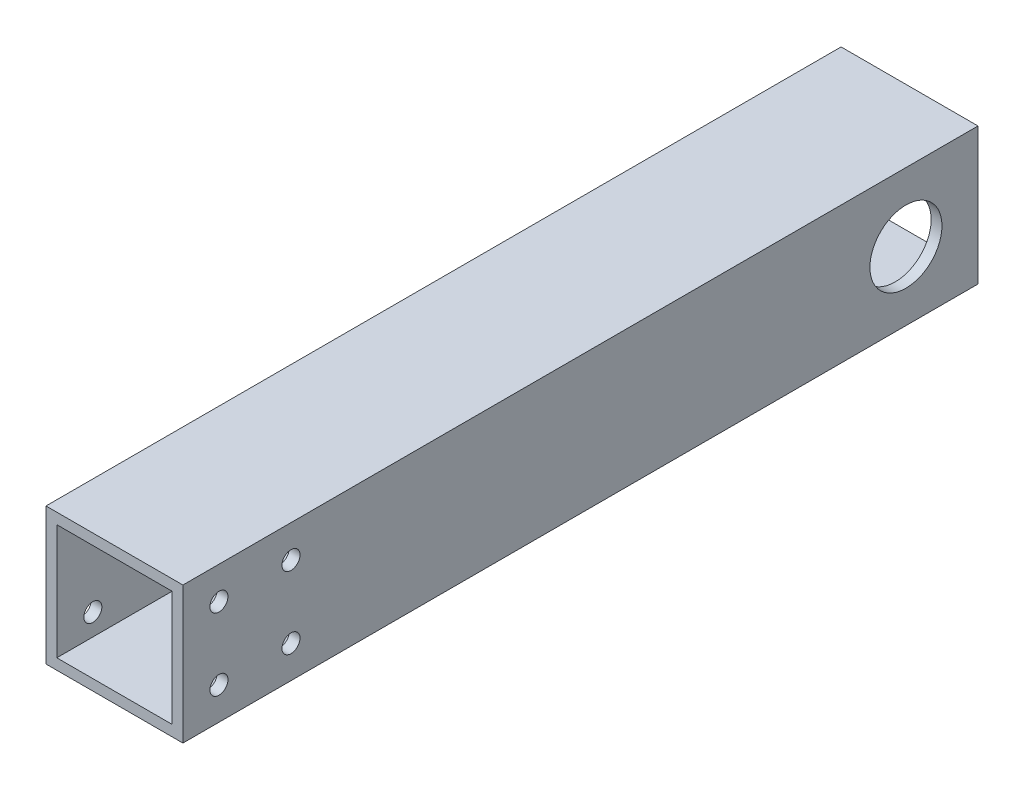
SolidWorks part; units mm, degrees
material "6061-T6 (SS)"
ref_plane "Front Plane" through (0, 0, 0) normal (0, 0, 1) x (1, 0, 0)
ref_plane "Top Plane" through (0, 0, 0) normal (0, 1, 0) x (1, 0, 0)
ref_plane "Right Plane" through (0, 0, 0) normal (1, 0, 0) x (0, 0, -1)
sketch "Sketch1" plane through (0, 0, 0) normal (0, 0, 1) x (1, 0, 0)
  line L0 (16, 16) -> (-16, 16)
  line L1 (19, -19) -> (-19, -19)
  line L2 (19, -19) -> (19, 19)
  line L3 (19, 19) -> (-19, 19)
  line L4 (-19, -19) -> (-19, 19)
  line L5 (19, -19) -> (-19, 19) construction
  line L6 (19, 19) -> (-19, -19) construction
  line L7 (-16, -16) -> (-16, 16)
  line L8 (16, -16) -> (-16, -16)
  line L9 (16, -16) -> (16, 16)
  point P0 (0, 0)
  dimension "D1" = 38
  dimension "D2" = 38
  dimension "D3" = 3
extrude "Boss-Extrude1" add sketch "Sketch1" along normal blind 220.68
sketch "Sketch2" plane through (-19, 0, 0) normal (-1, 0, 0) x (0, 0, 1)
  line L0 (220.68, 19) -> (220.68, -19) construction
  line L1 (190.68, -10) -> (210.68, -10) construction
  line L2 (190.68, -10) -> (190.68, 10) construction
  line L3 (190.68, 10) -> (210.68, 10) construction
  line L4 (210.68, -10) -> (210.68, 10) construction
  circle A4 centre (190.68, -10) radius 2.5
  circle A5 centre (210.68, -10) radius 2.5
  circle A6 centre (190.68, 10) radius 2.5
  circle A7 centre (210.68, 10) radius 2.5
  point P2 (190.68, 0)
  point P3 (220.68, 0)
  dimension "D1" = 5
  dimension "D2" = 10
  dimension "D3" = 20
extrude "Cut-Extrude1" cut sketch "Sketch2" against normal through all both and the other way through all
sketch "Sketch3" plane through (19, 0, 0) normal (1, 0, 0) x (0, 0, -1)
  line L0 (0, -19) -> (0, 19) construction
  circle A0 centre (-20, 0) radius 10
  dimension "D1" = 20
  dimension "D2" = 20
extrude "Cut-Extrude2" cut sketch "Sketch3" against normal through all
